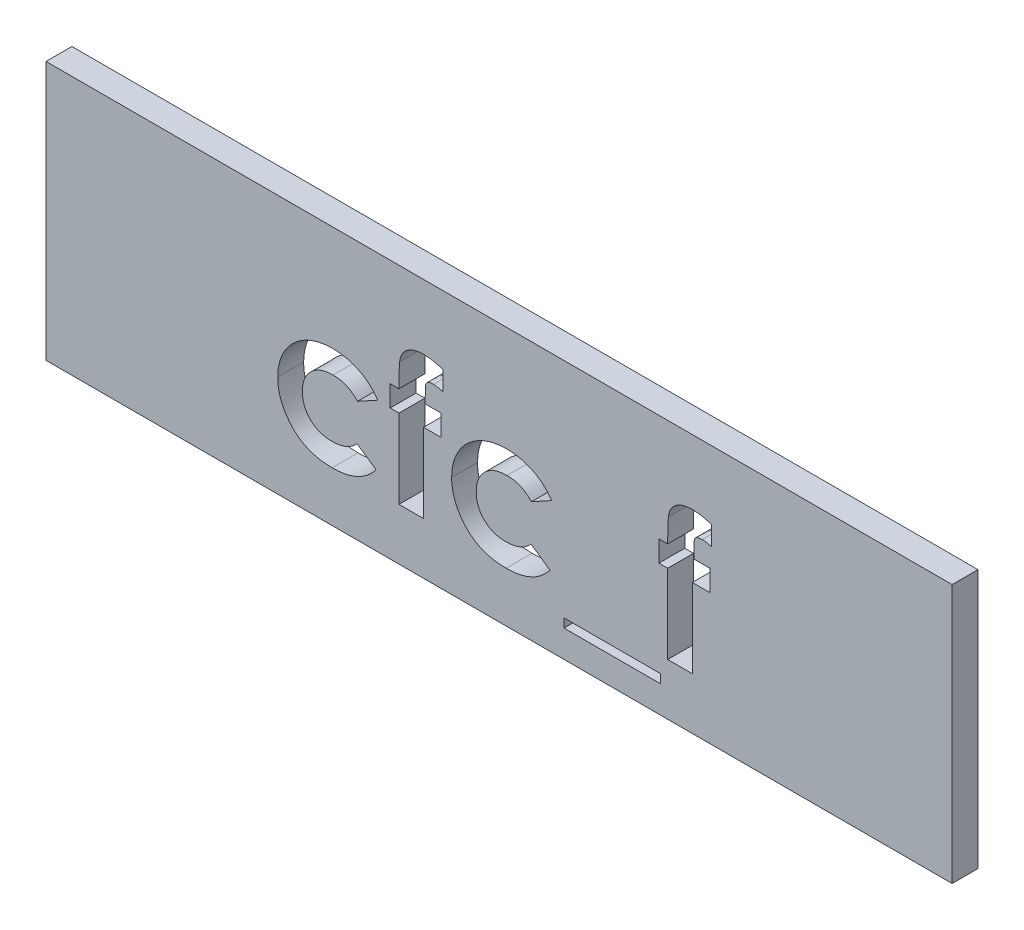
SolidWorks part; units mm, degrees
ref_plane "Plan de face" through (0, 0, 0) normal (0, 0, 1) x (1, 0, 0)
ref_plane "Plan de dessus" through (0, 0, 0) normal (0, 1, 0) x (1, 0, 0)
ref_plane "Plan de droite" through (0, 0, 0) normal (1, 0, 0) x (0, 0, -1)
sketch "Esquisse1" plane through (0, 0, 0) normal (0, 0, 1) x (1, 0, 0)
  line L1 (0, 0) -> (35, 0)
  line L2 (0, 0) -> (0, -10)
  line L3 (0, -10) -> (35, -10)
  line L4 (35, 0) -> (35, -10)
  dimension "D1" = 35
  dimension "D2" = 10
extrude "Boss.-Extru.1" add sketch "Esquisse1" along normal blind 1
sketch "Esquisse2" plane through (0, 0, 0) normal (0, 0, -1) x (-1, 0, 0)
  line L0 (-35, 0) -> (0, 0) construction
  line L1 (-35, -10) -> (-35, 0) construction
  line L2 (0, 0) -> (0, -10) construction
  circle A0 centre (-30, -5) radius 1
  circle A1 centre (-5, -5) radius 1
  dimension "D4" = 2
  dimension "D1" = 5
  dimension "D2" = 5
  dimension "D3" = 5
extrude "Boss.-Extru.2" add sketch "Esquisse2" along normal blind 3
chamfer "Chanfrein1" distance 0.5 angle 45 2 edges at (29, -5, -3) (4, -5, -3)
sketch "Esquisse3" plane through (0, 0, 1) normal (0, 0, 1) x (1, 0, 0)
  line L0 (7.5, -8) -> (27.5, -8) construction
  line L3 (0, -10) -> (35, -10) construction
  line L4 (0, 0) -> (0, -10) construction
  line L5 (35, -10) -> (35, 0) construction
  text T1 "<b>cfc_f</b>" font "Century Gothic" height in points 20
  point P12 (27.5, -8)
  dimension "D1" = 2
  dimension "D2" = 7.5
  dimension "D3" = 20
  dimension "D4" = 7.5
extrude "Enlèv. mat.-Extru.2" cut sketch "Esquisse3" against normal blind 1
